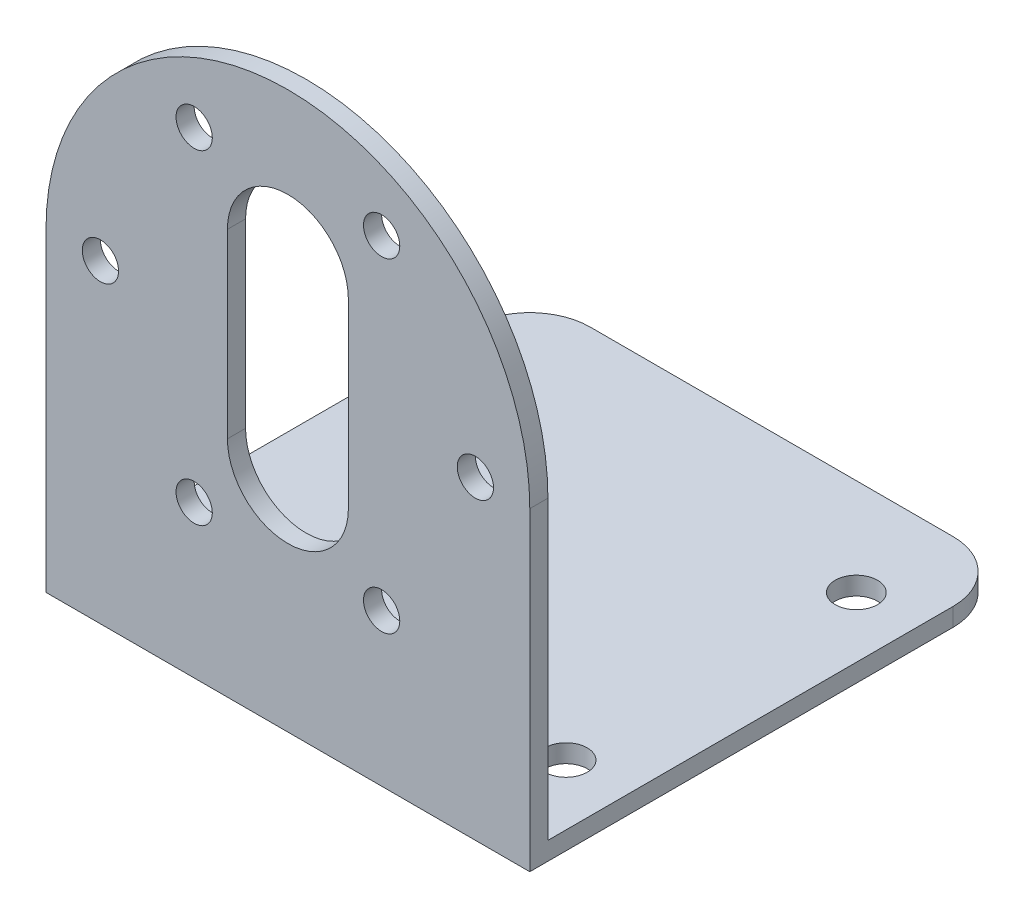
SolidWorks part; units mm, degrees
ref_plane "前视基准面" through (0, 0, 0) normal (0, 0, 1) x (1, 0, 0)
ref_plane "上视基准面" through (0, 0, 0) normal (0, 1, 0) x (1, 0, 0)
ref_plane "右视基准面" through (0, 0, 0) normal (1, 0, 0) x (0, 0, -1)
sketch "草图1" plane through (0, 0, 0) normal (0, 0, 1) x (1, 0, 0)
  line L2 (-20, 0) -> (-20, -26)
  line L3 (-20, -26) -> (20, -26)
  line L4 (20, 0) -> (20, -26)
  line L6 (5, -7.5) -> (5, 7.5)
  line L8 (-5, -7.5) -> (-5, 7.5)
  line L9 (5, -7.5) -> (-5, 7.5) construction
  line L10 (5, 7.5) -> (-5, -7.5) construction
  line L11 (7.75, 13.4234) -> (-7.75, 13.4234) construction
  line L12 (-7.75, 13.4234) -> (-15.5, 0) construction
  line L13 (-15.5, 0) -> (-7.75, -13.4234) construction
  line L14 (-7.75, -13.4234) -> (7.75, -13.4234) construction
  line L15 (7.75, -13.4234) -> (15.5, 0) construction
  line L16 (15.5, 0) -> (7.75, 13.4234) construction
  arc A0 (20, 0) -> (-20, 0) centre (0, 0) ccw
  circle A1 centre (0, 0) radius 15.5 construction
  arc A8 (-5, 7.5) -> (5, 7.5) centre (0, 7.5) cw
  arc A9 (-5, -7.5) -> (5, -7.5) centre (0, -7.5) ccw
  circle A10 centre (0, 0) radius 13.4234 construction
  circle A11 centre (7.75, 13.4234) radius 1.5
  circle A12 centre (-7.75, 13.4234) radius 1.5
  circle A13 centre (-15.5, 0) radius 1.5
  circle A14 centre (-7.75, -13.4234) radius 1.5
  circle A15 centre (7.75, -13.4234) radius 1.5
  circle A16 centre (15.5, 0) radius 1.5
  point P21 (0, 0)
  dimension "D2" = 15
  dimension "D3" = 10
extrude "凸台-拉伸1" add sketch "草图1" along normal blind 1.5
sketch "草图2" plane through (0, 0, 0) normal (0, 0, -1) x (-1, 0, 0)
  line L0 (20, 0) -> (20, -26) construction
  line L1 (-20, -26) -> (20, -26)
  line L2 (-20, -26) -> (-20, -24.5)
  line L3 (-20, -24.5) -> (20, -24.5)
  line L4 (20, -26) -> (20, -24.5)
extrude "凸台-拉伸2" add sketch "草图2" along normal blind 38.5
sketch "草图3" plane through (0, -26, 0) normal (0, -1, 0) x (1, 0, 0)
  line L0 (-20, 1.5) -> (20, -38.5) construction
  line L1 (-20, -38.5) -> (20, 1.5) construction
  line L3 (15, -30.5) -> (-15, -30.5) construction
  line L4 (15, -30.5) -> (15, -6.5) construction
  line L5 (15, -6.5) -> (-15, -6.5) construction
  line L6 (-15, -30.5) -> (-15, -6.5) construction
  line L7 (15, -30.5) -> (-15, -6.5) construction
  line L8 (15, -6.5) -> (-15, -30.5) construction
  circle A0 centre (-15, -6.5) radius 1.75
  circle A1 centre (15, -6.5) radius 1.75
  circle A2 centre (-15, -30.5) radius 1.75
  circle A3 centre (15, -30.5) radius 1.75
  point P8 (0, -18.5)
extrude "切除-拉伸1" cut sketch "草图3" against normal through all
fillet "圆角1" radius 5 2 edges at (-20, -25.25, -38.5) (20, -25.25, -38.5)
